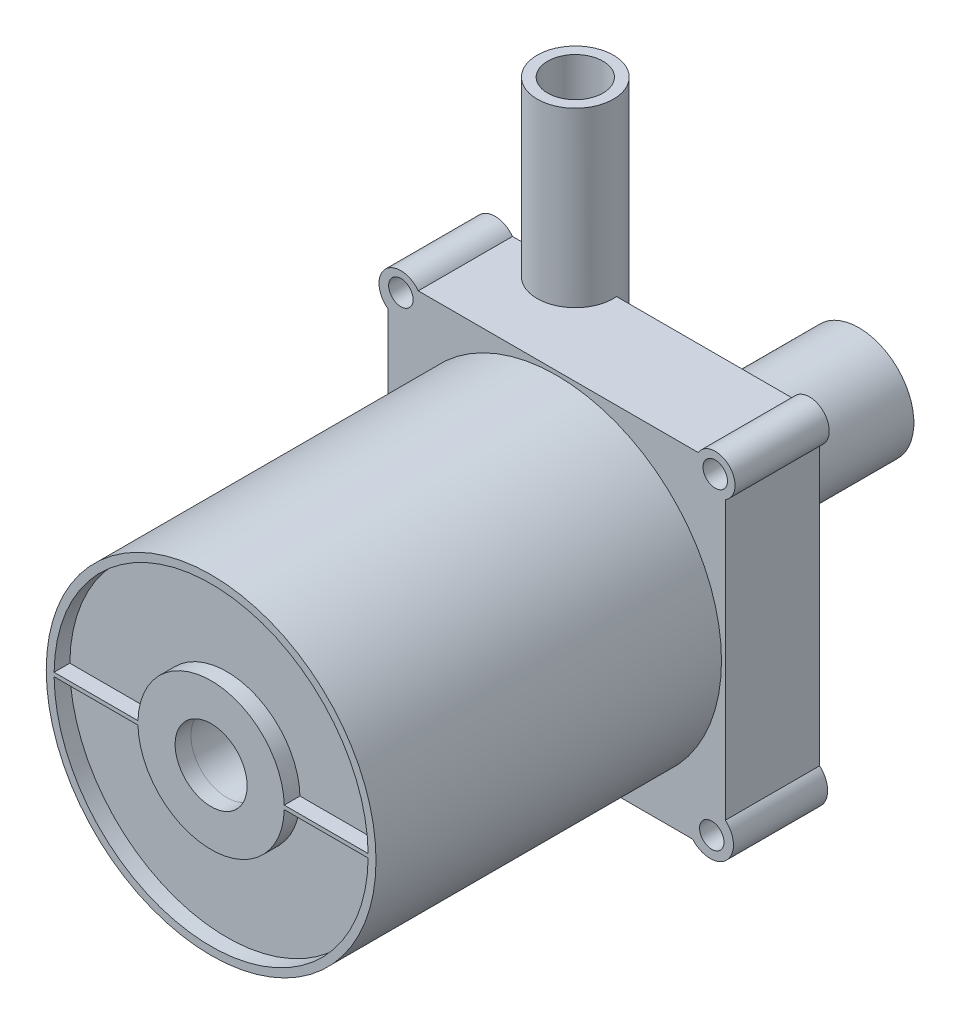
SolidWorks part; units mm, degrees
material "ABS"
ref_plane "Front Plane" through (0, 0, 0) normal (0, 0, 1) x (1, 0, 0)
ref_plane "Top Plane" through (0, 0, 0) normal (0, 1, 0) x (1, 0, 0)
ref_plane "Right Plane" through (0, 0, 0) normal (1, 0, 0) x (0, 0, -1)
sketch "Sketch2" plane through (0, 0, 0) normal (0, 0, 1) x (1, 0, 0)
  circle A0 centre (0, 0) radius 21
extrude "Boss-Extrude4" add sketch "Sketch2" along normal blind 44
sketch "Sketch5" plane through (0, 0, 44) normal (0, 0, 1) x (1, 0, 0)
  circle A0 centre (0, 0) radius 20.5
sketch "Sketch6" plane through (0, 0, 0) normal (0, 0, -1) x (-1, 0, 0)
  line L1 (-21.5, 21.5) -> (21.5, 21.5)
  line L2 (-21.5, 21.5) -> (-21.5, -21.5)
  line L3 (-21.5, -21.5) -> (21.5, -21.5)
  line L4 (21.5, 21.5) -> (21.5, -21.5)
  line L5 (-21.5, 21.5) -> (21.5, -21.5) construction
  line L6 (-21.5, -21.5) -> (21.5, 21.5) construction
  circle A0 centre (-20.202, 20.202) radius 2.521
  circle A1 centre (19.8464, 19.8464) radius 2.7742
  circle A2 centre (-19.5618, -19.5618) radius 2.9587
  circle A3 centre (19.8464, -19.8464) radius 3.1083
  point P0 (0, 0)
  circle M5 centre (0, 0) radius 21
  dimension "D1" = 43
  dimension "D2" = 43
extrude "Boss-Extrude8" add sketch "Sketch6" along normal blind 12 contours A3 L4 A1 L1 A0 L2 A2 L3 M5 | L3 A2 L2 | L4 A3 L3 | L3 A3 L4
sketch "Sketch7" plane through (0, 0, -12) normal (0, 0, -1) x (-1, 0, 0)
  circle A0 centre (-20.202, 20.202) radius 1.558
  circle A1 centre (19.8326, 20.202) radius 1.558
  circle A2 centre (19.8464, -19.8464) radius 1.558
  circle A3 centre (-19.7621, -19.8464) radius 1.558
  dimension "D1" = 3.116
extrude "Cut-Extrude1" cut sketch "Sketch7" against normal blind 12
sketch "Sketch9" plane through (0, 0, -12) normal (0, 0, -1) x (-1, 0, 0)
  circle A0 centre (0, 0) radius 14.25
extrude "Boss-Extrude10" add sketch "Sketch9" along normal blind 4.5
sketch "Sketch10" plane through (0, 21.5, 0) normal (0, 1, 0) x (1, 0, 0)
  circle A0 centre (-9.1927, 11.5736) radius 4.856
extrude "Boss-Extrude12" add sketch "Sketch10" along normal blind 22 and the other way blind 22
sketch "Sketch11" plane through (0, 0, -16.5) normal (0, 0, -1) x (-1, 0, 0)
  circle A0 centre (0, 0) radius 9
extrude "Boss-Extrude13" add sketch "Sketch11" along normal blind 6
sketch "Sketch12" plane through (0, 0, -22.5) normal (0, 0, -1) x (-1, 0, 0)
  circle A0 centre (0, 0) radius 7
extrude "Boss-Extrude14" add sketch "Sketch12" along normal blind 16
sketch "Sketch13" plane through (0, 0, -38.5) normal (0, 0, -1) x (-1, 0, 0)
  circle A0 centre (0, 0) radius 4.6705
extrude "Cut-Extrude3" cut sketch "Sketch13" against normal blind 120
sketch "Sketch15" plane through (0, 43.5, 0) normal (0, 1, 0) x (1, 0, 0)
  circle A0 centre (-9.1927, 11.5736) radius 3.5271
extrude "Cut-Extrude5" cut sketch "Sketch15" against normal blind 40
sketch "Sketch16" plane through (0, 0, 44) normal (0, 0, 1) x (1, 0, 0)
  circle A0 centre (0, 0) radius 20
extrude "Cut-Extrude6" cut sketch "Sketch16" against normal blind 2
sketch "Sketch17" plane through (0, 0, 42) normal (0, 0, 1) x (1, 0, 0)
  line L1 (-20.4985, 0.2453) -> (20.4985, 0.2453)
  line L2 (-20.4985, 0.2453) -> (-20.4985, -0.2453)
  line L3 (-20.4985, -0.2453) -> (20.4985, -0.2453)
  line L4 (20.4985, 0.2453) -> (20.4985, -0.2453)
  line L5 (-20.4985, 0.2453) -> (20.4985, -0.2453) construction
  line L6 (-20.4985, -0.2453) -> (20.4985, 0.2453) construction
  circle A0 centre (0, 0) radius 20.5 construction
  point P0 (0, 0)
extrude "Boss-Extrude15" add sketch "Sketch17" along normal blind 2
sketch "Sketch18" plane through (0, 0, 42) normal (0, 0, 1) x (1, 0, 0)
  circle A0 centre (0, 0) radius 9.3194
extrude "Boss-Extrude16" add sketch "Sketch18" along normal blind 2
sketch "Sketch19" plane through (0, 0, 44) normal (0, 0, 1) x (1, 0, 0)
  circle A0 centre (0, 0) radius 4.5823
extrude "Cut-Extrude7" cut sketch "Sketch19" against normal blind 2
